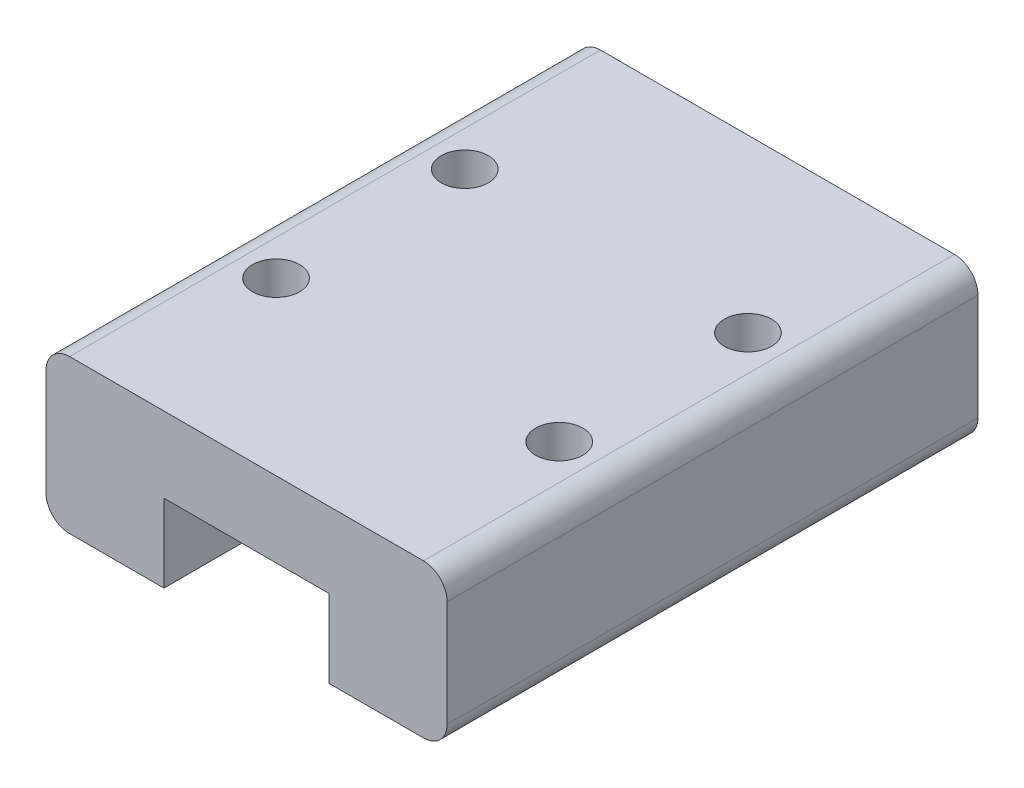
SolidWorks part; units mm, degrees
other "细节项目1"
ref_plane "Front" through (0, 0, 0) normal (0, 0, 1) x (1, 0, 0)
ref_plane "Top" through (0, 0, 0) normal (0, 1, 0) x (1, 0, 0)
ref_plane "Right" through (0, 0, 0) normal (1, 0, 0) x (0, 0, -1)
sketch "草图1" plane through (0, 0, 0) normal (0, 0, 1) x (1, 0, 0)
  line L0 (5, 3.3) -> (12, 3.3)
  line L1 (1, 0) -> (5, 0)
  line L2 (0, 1) -> (0, 5.5)
  line L3 (1, 6.5) -> (16, 6.5)
  line L4 (17, 1) -> (17, 5.5)
  line L5 (5, 0) -> (5, 3.3)
  line L6 (12, 0) -> (12, 3.3)
  line L7 (12, 0) -> (16, 0)
  line L8 (5, 0) -> (5, 6.5) construction
  line L9 (0, 3.3) -> (17, 3.3) construction
  line L10 (12, 0) -> (12, 6.5) construction
  line L11 (0, 6.5) -> (17, 6.5) construction
  line L12 (17, 0) -> (17, 6.5) construction
  line L13 (0, 0) -> (0, 6.5) construction
  arc A0 (16, 6.5) -> (17, 5.5) centre (16, 5.5) cw
  arc A1 (0, 5.5) -> (1, 6.5) centre (1, 5.5) cw
  arc A2 (16, 0) -> (17, 1) centre (16, 1) ccw
  arc A3 (1, 0) -> (0, 1) centre (1, 1) cw
  dimension "D4" = 1
  dimension "D5" = 1
  dimension "D6" = 1
  dimension "D7" = 1
  dimension "D1" = 3.2
  dimension "D2" = 5
  dimension "D3" = 5
extrude "凸台-拉伸1" add sketch "草图1" along normal blind 22.5
sketch "草图2" plane through (0, 6.5, 0) normal (0, 1, 0) x (1, 0, 0)
  line L5 (1, -22.5) -> (1, 0) construction
  line L6 (16, -22.5) -> (16, 0) construction
  circle A0 centre (2.5, -15.25) radius 1
  circle A1 centre (2.5, -7.25) radius 1
  circle A2 centre (14.5, -7.25) radius 1
  circle A3 centre (14.5, -15.25) radius 1
  dimension "D5" = 1.5
  dimension "D6" = 1.5
  dimension "D7" = 1.5
  dimension "D8" = 1.5
extrude "切除-拉伸1" cut sketch "草图2" against normal blind 2.5
